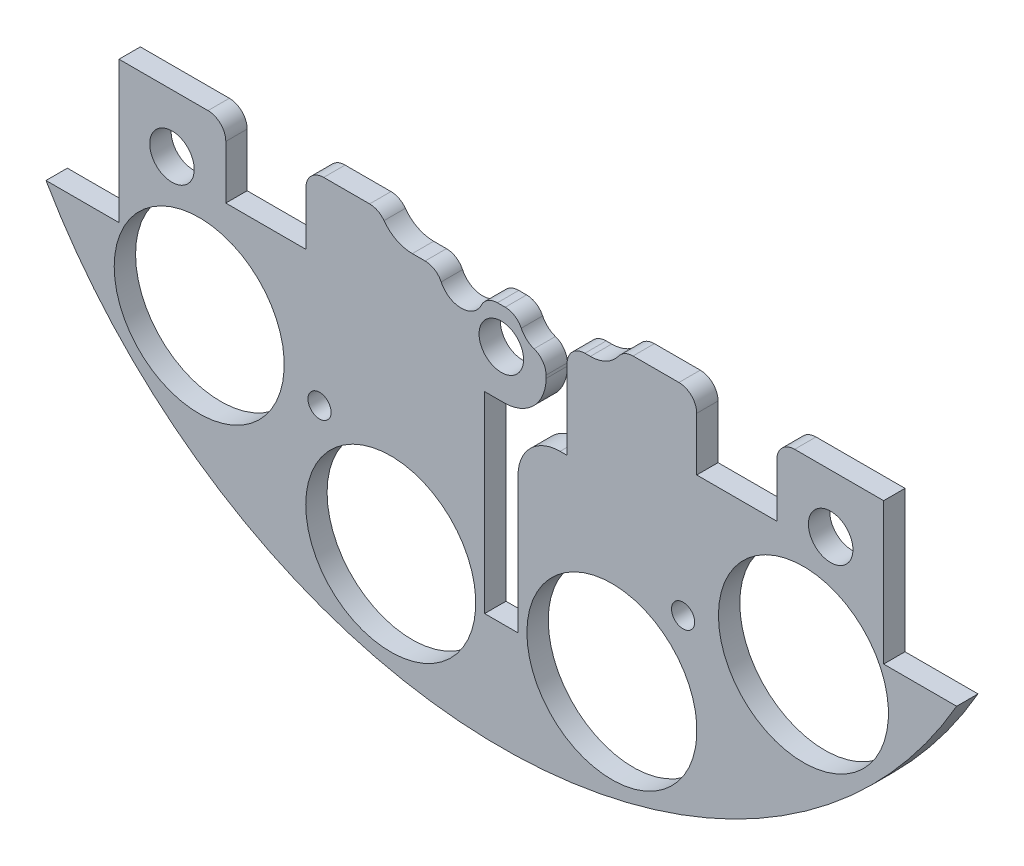
SolidWorks part; units mm, degrees
ref_plane "Front Plane" through (0, 0, 0) normal (0, 0, 1) x (1, 0, 0)
ref_plane "Top Plane" through (0, 0, 0) normal (0, 1, 0) x (1, 0, 0)
ref_plane "Right Plane" through (0, 0, 0) normal (1, 0, 0) x (0, 0, -1)
sketch "Sketch1" plane through (0, 0, 0) normal (0, 0, 1) x (1, 0, 0)
  line L0 (0, 0) -> (-82.1241, 0) construction
  line L1 (0, 0) -> (0, 95.6219) construction
  line L3 (-64.9644, 37.338) -> (-54.5504, 37.338)
  line L5 (-64.9644, -37.338) -> (-54.5504, -37.338)
  line L6 (-54.5504, 37.338) -> (-54.5504, -37.338)
  line L7 (64.9644, -37.338) -> (54.5504, -37.338)
  line L8 (64.9644, 37.338) -> (54.5504, 37.338)
  line L9 (54.5504, 37.338) -> (54.5504, -37.338)
  arc A0 (-64.9644, -37.338) -> (64.9644, -37.338) centre (0, 0) ccw
  circle A1 centre (-46.482, 11.049) radius 1.651
  circle A2 centre (-21.0833, 10.795) radius 1.651
  circle A3 centre (-21.0833, -10.795) radius 1.651
  circle A4 centre (-46.482, -11.049) radius 1.651
  circle A5 centre (46.482, -11.049) radius 1.651
  circle A6 centre (21.0833, -10.795) radius 1.651
  circle A7 centre (21.0833, 10.795) radius 1.651
  circle A8 centre (46.482, 11.049) radius 1.651
  arc A9 (64.9644, 37.338) -> (-64.9644, 37.338) centre (0, 0) ccw
  dimension "D2" = 3.302
  dimension "D3" = 3.302
  dimension "D4" = 25.4
  dimension "D5" = 10.795
  dimension "D10" = 46.482
  dimension "D6" = 74.676
  dimension "D7" = 10.414
  dimension "D8" = 74.93
  dimension "D9" = 74.93
  dimension "D11" = 37.338
extrude "Boss-Extrude2" add sketch "Sketch1" along normal blind 3.048
sketch "Sketch2" plane through (0, 0, 3.048) normal (0, 0, 1) x (1, 0, 0)
  line L0 (0, 68.58) -> (0, 55.88) construction
  line L1 (-9.525, 68.58) -> (9.525, 68.58)
  line L2 (-9.525, 68.58) -> (-9.525, 55.88)
  line L3 (-9.525, 55.88) -> (9.525, 55.88)
  line L4 (9.525, 68.58) -> (9.525, 55.88)
  line L5 (-9.525, 62.23) -> (9.525, 62.23) construction
  arc A0 (64.9644, 37.338) -> (-64.9644, 37.338) centre (0, 0) ccw construction
  circle A1 centre (-21.0833, 10.795) radius 1.651 construction
  circle A2 centre (21.0833, 10.795) radius 1.651 construction
  circle A3 centre (-6.731, 62.23) radius 1.143
  circle A4 centre (6.731, 62.23) radius 1.143
  dimension "D4" = 2.286
  dimension "D5" = 0
  dimension "D6" = 6.731
  dimension "D1" = 19.05
  dimension "D2" = 12.7
  dimension "D3" = 55.88
extrude "Cut-Extrude1" cut sketch "Sketch2" against normal through all contours A3 | A4
sketch "Sketch3" plane through (0, 0, 0) normal (0, 0, -1) x (-1, 0, 0)
  line L0 (0, 0) -> (0, -116.2908) construction
  line L1 (0, 0) -> (-153.8039, 0) construction
  line L2 (0, 0) -> (15.2681, -56.9814) construction
  line L3 (0, 0) -> (15.2302, -26.3795) construction
  circle A0 centre (-15.7776, -58.8828) radius 12.1285
  circle A3 centre (15.7776, -58.8828) radius 12.1285
  circle A4 centre (-43.1052, -43.1052) radius 12.1285
  circle A7 centre (19.05, 32.9956) radius 12.1285
  circle A8 centre (-43.1052, 43.1052) radius 12.1285
  circle A11 centre (43.1052, 43.1052) radius 12.1285
  circle A12 centre (-19.05, 32.9956) radius 12.1285
  circle A14 centre (43.1052, -43.1052) radius 12.1285
  circle A33 centre (58.8828, -15.7776) radius 12.1285 [skipped]
  circle A34 centre (58.8828, 15.7776) radius 12.1285 [skipped]
  circle A35 centre (-58.8828, 15.7776) radius 12.1285 [skipped]
  circle A36 centre (-58.8828, -15.7776) radius 12.1285 [skipped]
  circle A37 centre (-15.7776, 58.8828) radius 12.1285 [skipped]
  circle A38 centre (15.7776, 58.8828) radius 12.1285 [skipped]
  point P36 (0, 0)
  point P53 (0, 0)
  point P55 (0, 0)
  dimension "D3" = 0
  dimension "D4" = 15
  dimension "D5" = 24.257
  dimension "D7" = 12
  dimension "D9" = 30
extrude "Cut-Extrude2" cut sketch "Sketch3" against normal through all
sketch "Sketch4" plane through (0, 0, 0) normal (0, 0, -1) x (-1, 0, 0)
  line L1 (-15.7702, 56.3138) -> (12.7925, 56.3138)
  line L2 (-15.7702, 56.3138) -> (-15.7702, 67.9913)
  line L3 (-15.7702, 67.9913) -> (12.7925, 67.9913)
  line L4 (12.7925, 56.3138) -> (12.7925, 67.9913)
extrude "Boss-Extrude3" add sketch "Sketch4" against normal up to surface (3.048 mm away) up to face at (-55.2337, -43.1052, 3.048)
sketch "Sketch5" plane through (0, 0, 0) normal (0, 0, -1) x (-1, 0, 0)
  line L1 (-85.044, -17.145) -> (131.6774, -17.145)
  line L2 (-85.044, -17.145) -> (-85.044, 113.4242)
  line L3 (-85.044, 113.4242) -> (131.6774, 113.4242)
  line L4 (131.6774, -17.145) -> (131.6774, 113.4242)
  circle A0 centre (-21.0833, -10.795) radius 1.651 construction
  dimension "D1" = 6.35
extrude "Cut-Extrude4" cut sketch "Sketch5" against normal through all contours L2 L3 L4 L1
sketch "Sketch6" plane through (0, 0, 0) normal (0, 0, -1) x (-1, 0, 0)
  line L1 (-54.5504, -17.145) -> (54.5504, -17.145) construction
  line L2 (-2.3812, -32.131) -> (-6.3812, -32.131)
  line L3 (-6.3812, -32.131) -> (-6.3812, -17.145)
  line L4 (-6.3812, -17.145) -> (-9.3812, -17.145)
  line L5 (-9.3812, -17.145) -> (-9.3812, -34.131)
  line L6 (2.3813, -59.563) -> (-2.3812, -59.563)
  line L7 (2.3813, -59.563) -> (2.3813, -32.131)
  line L8 (2.3813, -32.131) -> (-2.3812, -32.131)
  line L9 (-2.3812, -59.563) -> (-2.3812, -32.131)
  line L10 (-9.3812, -34.131) -> (-2.3812, -34.131)
  line M13 (54.5504, -17.145) -> (-54.5504, -17.145)
  dimension "D1" = 42.418
  dimension "D2" = 3
  dimension "D3" = 2
  dimension "D4" = 4
  dimension "D5" = 27.432
  dimension "D6" = 4.7625
extrude "Cut-Extrude5" cut sketch "Sketch6" against normal through all contours L9 L6 L7 L8 | L5 L10 L9 L2 L3 M13
extrude "Cut-Extrude6" cut sketch "Sketch7" against normal through all both and the other way through all
sketch "Sketch7" plane through (31.3134, 132.614, -9.525) normal (0, 0, -1) x (0, 1, 0)
  line L0 (-132.614, -31.3134) -> (-132.614, 57.8454) construction
  line L1 (-132.614, -31.3134) -> (-222.516, -31.3134) construction
  circle A0 centre (-158.014, 14.4066) radius 3.175
  circle A1 centre (-173.254, -31.3134) radius 3.175
  circle A3 centre (-158.014, -77.0334) radius 3.175
  circle A4 centre (-107.214, -77.0334) radius 3.175
  circle A5 centre (-91.974, -31.3134) radius 3.175
  circle A6 centre (-107.214, 14.4066) radius 3.175
extrude "Cut-Extrude7" cut sketch "Sketch8" against normal blind 29.21
sketch "Sketch8" plane through (31.3134, 132.559, -6.35) normal (0, 0, -1) x (0, 1, 0)
  line L0 (-132.559, -31.3134) -> (6.1626, -31.3134) construction
  line L2 (-132.559, -31.3134) -> (-132.559, -122.6589) construction
  circle A0 centre (-190.979, 2.9766) radius 1.651
  circle A2 centre (-154.784, -31.3134) radius 1.651
  circle A3 centre (-190.979, -65.6034) radius 1.651
  circle A4 centre (-110.334, -31.3134) radius 1.651
  circle A5 centre (-74.139, -65.6034) radius 1.651
  circle A6 centre (-74.139, 2.9766) radius 1.651
sketch "Sketch10" plane through (0, 0, 0) normal (0, 0, -1) x (-1, 0, 0)
  line L0 (-54.5504, -17.145) -> (-9.3812, -17.145) construction
  line L1 (-39.3104, -17.145) -> (-27.8804, -17.145)
  line L2 (-39.3104, -17.145) -> (-39.3104, -27.305)
  line L3 (-39.3104, -27.305) -> (-27.8804, -27.305)
  line L4 (-27.8804, -17.145) -> (-27.8804, -27.305)
  line L5 (-6.3812, -17.145) -> (54.5504, -17.145) construction
  line L6 (27.8804, -17.145) -> (39.3104, -17.145)
  line L7 (27.8804, -17.145) -> (27.8804, -27.305)
  line L8 (27.8804, -27.305) -> (39.3104, -27.305)
  line L9 (39.3104, -17.145) -> (39.3104, -27.305)
  line L10 (-54.5504, -37.338) -> (-54.5504, -17.145) construction
  line L11 (0, -3.5331) -> (0, -80.5859) construction
  dimension "D1" = 10.16
  dimension "D2" = 11.43
  dimension "D3" = 15.24
extrude "Cut-Extrude9" cut sketch "Sketch10" against normal through all
fillet "Fillet1" radius 6 1 edges at (6.3812, -32.131, 1.524)
fillet "Fillet2" radius 6 1 edges at (2.3812, -34.131, 1.524)
extrude "Cut-Extrude65" cut sketch "Sketch66" against normal blind 97.79
sketch "Sketch66" plane through (30.092, 4.0835, -16.1925) normal (0, 0, -1) x (-1, 0, 0)
  line L0 (30.092, -29.4835) -> (30.092, 6.2385) construction
  circle A0 centre (4.1544, -49.7288) radius 1.651
  circle A4 centre (56.0296, -49.7288) radius 1.651
  circle A5 centre (4.1544, 41.3825) radius 1.651
  circle A9 centre (56.0296, 41.3825) radius 1.651
extrude "Cut-Extrude119" cut sketch "Sketch120" against normal blind 48.768 and the other way blind 103.378
sketch "Sketch120" plane through (30.092, 4.0835, 19.939) normal (0, 0, -1) x (-1, 0, 0)
  line L0 (30.092, -4.0835) -> (148.6336, -4.0835) construction
  line L1 (30.092, -4.0835) -> (30.092, 90.452) construction
  circle A0 centre (-16.898, 21.3165) radius 3.175
  circle A1 centre (77.082, 21.3165) radius 3.175
  circle A2 centre (30.092, 21.3165) radius 3.175
  circle A4 centre (77.082, -29.4835) radius 3.175
  circle A5 centre (30.092, -29.4835) radius 3.175
  circle A6 centre (-16.898, -29.4835) radius 3.175
sketch "Sketch13" plane through (0, 0, 0) normal (0, 0, -1) x (-1, 0, 0)
  line L0 (0, 0) -> (0, 51.5587) construction
  line L1 (-9.3812, -17.145) -> (-9.3812, -34.131) construction
  line L2 (-12.7, -20.24) -> (-8.889, -20.24)
  line L3 (-2.541, -20.24) -> (2.541, -20.24)
  line L4 (-1.0625, -15.24) -> (7.7, -15.24)
  line L5 (8.889, -20.24) -> (12.7, -20.24)
  arc A0 (-9.3812, -11.5002) -> (-12.7, -20.24) centre (-12.7, -15.24) ccw
  arc A1 (7.7, -15.24) -> (12.7, -20.24) centre (12.7, -15.24) cw
  arc A2 (-9.3812, -11.5002) -> (-1.0625, -15.24) centre (-6.0625, -15.24) cw
  arc A3 (-8.889, -20.24) -> (-2.541, -20.24) centre (-5.715, -20.32) ccw
  arc A4 (2.541, -20.24) -> (8.889, -20.24) centre (5.715, -20.32) ccw
  dimension "D1" = 10
  dimension "D4" = 11.43
  dimension "D5" = 6.35
  dimension "D6" = 6.35
  dimension "D2" = 12.7
  dimension "D3" = 15.24
  dimension "D7" = 5.715
  dimension "D8" = 20.32
extrude "Cut-Extrude12" cut sketch "Sketch13" against normal blind 10
fillet "Fillet3" radius 2.54 11 edges at (-39.3104, -17.145, 1.524) (-27.8804, -17.145, 1.524) (-17.3229, -17.145, 1.524) (-8.889, -20.24, 1.524) (2.541, -20.24, 1.524) (-2.541, -20.24, 1.524) (6.3812, -23.4243, 1.524) (9.3812, -20.24, 1.524) (17.3229, -17.145, 1.524) (27.8804, -17.145, 1.524) (39.3104, -17.145, 1.524)
